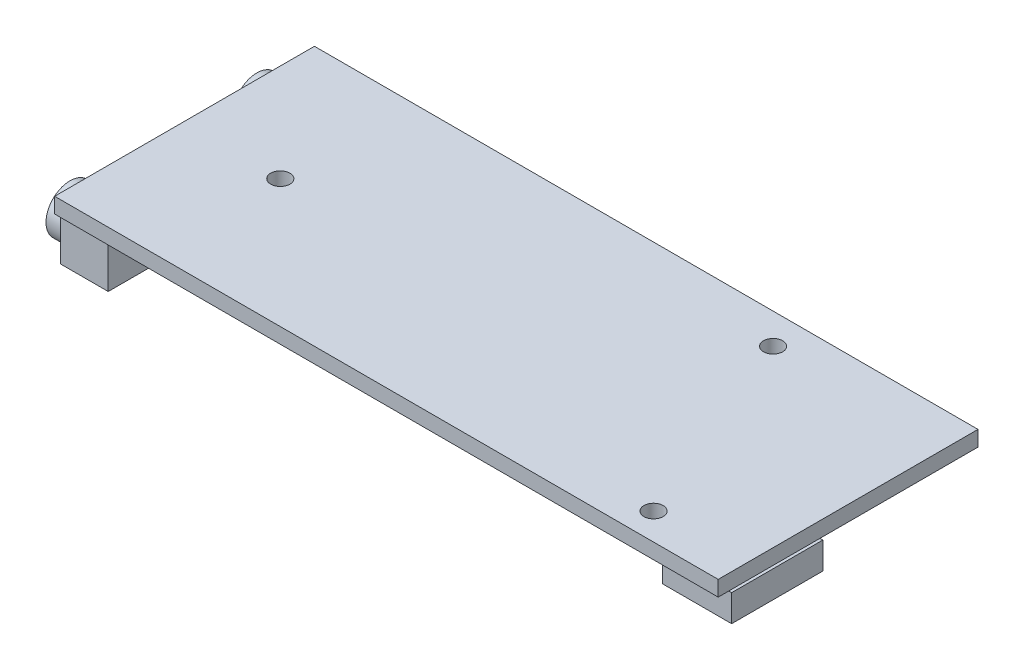
SolidWorks part; units mm, degrees
ref_plane "Front" through (0, 0, 0) normal (0, 0, 1) x (1, 0, 0)
ref_plane "Top" through (0, 0, 0) normal (0, 1, 0) x (1, 0, 0)
ref_plane "Right" through (0, 0, 0) normal (1, 0, 0) x (0, 0, -1)
sketch "Sketch1" plane through (0, 0, 0) normal (0, 1, 0) x (1, 0, 0)
  line L1 (0, 0) -> (69.088, 0)
  line L2 (0, 0) -> (0, -27.051)
  line L3 (0, -27.051) -> (69.088, -27.051)
  line L4 (69.088, 0) -> (69.088, -27.051)
  dimension "D1" = 69.088
  dimension "D2" = 27.051
extrude "Boss-Extrude1" add sketch "Sketch1" along normal blind 1.6
sketch "Sketch2" plane through (0, 0, 0) normal (0, -1, 0) x (-1, 0, 0)
  line L0 (-69.088, 0) -> (0, 0) construction
  line L1 (0.2, -26.251) -> (-4.779, -26.251)
  line L2 (0.2, -26.251) -> (0.2, -20.251)
  line L3 (0.2, -20.251) -> (-4.779, -20.251)
  line L4 (-4.779, -26.251) -> (-4.779, -20.251)
  line L5 (0.2, -6.8) -> (-4.779, -6.8)
  line L6 (0.2, -6.8) -> (0.2, -0.8)
  line L7 (0.2, -0.8) -> (-4.779, -0.8)
  line L8 (-4.779, -6.8) -> (-4.779, -0.8)
  line L9 (0.8044, -17.0411) -> (-3.0576, -17.0411)
  line L10 (0.8044, -17.0411) -> (0.8044, -11.1819)
  line L11 (0.8044, -11.1819) -> (-3.0576, -11.1819)
  line L12 (-3.0576, -17.0411) -> (-3.0576, -11.1819)
  line L13 (0, -27.051) -> (-69.088, -27.051) construction
  line L14 (0, 0) -> (0, -27.051) construction
  dimension "D1" = 6
  dimension "D2" = 6
  dimension "D3" = 6.8
  dimension "D4" = 0.8
  dimension "D5" = 0.2
  dimension "D6" = 0.2
extrude "Boss-Extrude2" add sketch "Sketch2" along normal blind 5
sketch "Sketch3" plane through (0, 0, 0) normal (0, -1, 0) x (-1, 0, 0)
  line L0 (-69.088, -27.051) -> (-69.088, 0) construction
  line L1 (-57.588, -2.129) -> (-64.088, -2.129)
  line L2 (-57.588, -2.129) -> (-57.588, 0.5885)
  line L3 (-57.588, 0.5885) -> (-64.088, 0.5885)
  line L4 (-64.088, -2.129) -> (-64.088, 0.5885)
  dimension "D1" = 5
  dimension "D2" = 6.5
extrude "Boss-Extrude3" add sketch "Sketch3" along normal blind 2
sketch "Sketch4" plane through (0, 0, 0) normal (0, -1, 0) x (-1, 0, 0)
  line L0 (0, -27.051) -> (-69.088, -27.051) construction
  line L1 (-62.2085, -25.951) -> (-69.388, -25.951)
  line L2 (-62.2085, -25.951) -> (-62.2085, -16.451)
  line L3 (-62.2085, -16.451) -> (-69.388, -16.451)
  line L4 (-69.388, -25.951) -> (-69.388, -16.451)
  line L5 (-69.088, -27.051) -> (-69.088, 0) construction
  dimension "D1" = 1.1
  dimension "D2" = 9.5
  dimension "D3" = 0.3
extrude "Boss-Extrude4" add sketch "Sketch4" along normal blind 2.8
sketch "Sketch5" plane through (0, 0, 0) normal (0, -1, 0) x (-1, 0, 0)
  line L0 (-69.088, -16.451) -> (-69.088, 0) construction
  line L1 (0, -27.051) -> (-69.088, -27.051) construction
  circle A0 centre (-59.563, -24.257) radius 1
  circle A1 centre (-50.927, -3.175) radius 1
  circle A2 centre (-10.16, -13.716) radius 1
  dimension "D1" = 18.161
  dimension "D5" = 13.335
  dimension "D7" = 2
  dimension "D8" = 2
  dimension "D9" = 2
  dimension "D2" = 23.876
  dimension "D3" = 2.794
  dimension "D4" = 9.525
  dimension "D6" = 58.928
extrude "Cut-Extrude1" cut sketch "Sketch5" against normal through all
sketch "Sketch6" plane through (0, 0, 0) normal (0, -1, 0) x (-1, 0, 0)
  circle A0 centre (-59.8075, -7.2513) radius 1.6898
extrude "Boss-Extrude5" add sketch "Sketch6" along normal blind 4
sketch "Sketch7" plane through (0, 0, 0) normal (0, -1, 0) x (-1, 0, 0)
  circle A0 centre (-59.4387, -16.9206) radius 0.9175
extrude "Boss-Extrude6" add sketch "Sketch7" along normal blind 4.5
sketch "Sketch8" plane through (-0.2, 0, 0) normal (-1, 0, 0) x (0, 0, 1)
  line L0 (26.251, -5) -> (20.251, -5) construction
  line L2 (0.8, -5) -> (0.8, 0) construction
  line L3 (6.8, -5) -> (0.8, -5) construction
  line L4 (20.251, -5) -> (20.251, 0) construction
  circle A0 centre (3.8, -2.5) radius 2.5
  circle A1 centre (23.251, -2.5) radius 2.5
  point P6 (0, 0)
  dimension "D3" = 5
  dimension "D6" = 5
  dimension "D1" = 3
  dimension "D2" = 2.5
  dimension "D4" = 3
  dimension "D5" = 2.5
extrude "Boss-Extrude7" add sketch "Sketch8" along normal blind 2
